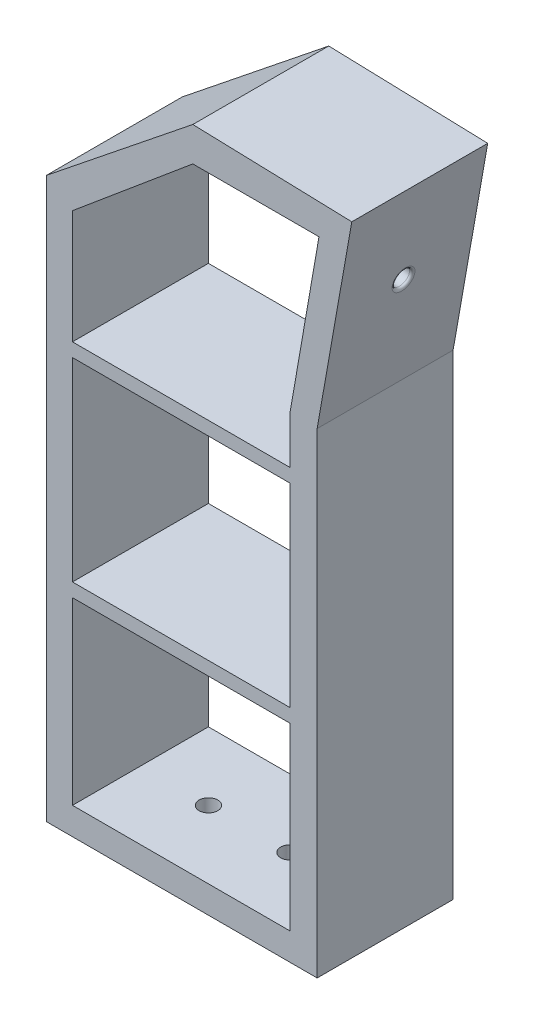
SolidWorks part; units mm, degrees
ref_plane "Front Plane" through (0, 0, 0) normal (0, 0, 1) x (1, 0, 0)
ref_plane "Top Plane" through (0, 0, 0) normal (0, 1, 0) x (1, 0, 0)
ref_plane "Right Plane" through (0, 0, 0) normal (1, 0, 0) x (0, 0, -1)
sketch "Sketch2" plane through (0, 0, 0) normal (0, 0, 1) x (1, 0, 0)
  line L8 (-40.5065, 0) -> (59.131, 0)
  line L10 (59.131, 232.5877) -> (59.801, 236.4462)
  line L12 (59.131, 0) -> (59.131, 175)
  line L14 (59.131, 175) -> (59.131, 265.8716) construction
  line L16 (-40.869, 107.9897) -> (-30.869, 107.9897) construction
  line L17 (65.5005, 211.1233) -> (55.5005, 211.1233) construction
  line L18 (59.131, 87.5) -> (49.131, 87.5) construction
  line L19 (0, 0) -> (0, 10) construction
  line L20 (0, 10) -> (49.131, 10)
  line L21 (49.131, 10) -> (49.131, 87.5)
  line L22 (49.131, 87.5) -> (49.131, 175)
  line L23 (-40.5065, 205.8291) -> (-40.5065, 0)
  line L28 (-30.869, 107.9897) -> (-30.869, 10)
  line L29 (-30.869, 10) -> (0, 10)
  line L30 (59.131, 175) -> (71.87, 247.2467)
  line L32 (-30.869, 107.9897) -> (-30.869, 199.4173)
  line L34 (59.131, 232.5877) -> (49.131, 175)
  line L35 (59.131, 232.5877) -> (68.9791, 230.8512) construction
  line L36 (71.87, 247.2467) -> (13.3973, 249.0046)
  line L37 (13.3973, 249.0046) -> (-40.5065, 205.8291)
  line L38 (42.6337, 248.1256) -> (42.6337, 236.4462) construction
  line L39 (-30.869, 199.4173) -> (6.2516, 230.4687)
  line L40 (59.801, 236.4462) -> (42.6337, 236.4462)
  line L41 (42.6337, 236.4462) -> (13.3973, 236.4462)
  line L44 (13.3973, 249.0046) -> (13.3973, 239.0046) construction
  line L46 (0, 238.2737) -> (6.2516, 230.4687) construction
  line L47 (6.2516, 230.4687) -> (13.3973, 236.4462)
  point P1 (9.131, 107.9897)
  dimension "D1" = 10
  dimension "D2" = 9.131
  dimension "D3" = 49.131
  dimension "D4" = 59.131
  dimension "D5" = 71.87
  dimension "D6" = 30.869
  dimension "D7" = 40.5065
  dimension "D8" = 175
extrude "Boss-Extrude1" add sketch "Sketch2" along normal blind 50
sketch "Sketch10" plane through (0, 10, 0) normal (0, 1, 0) x (1, 0, 0)
  line L0 (49.131, -25) -> (24.131, -25) construction
  line L1 (-30.869, -50) -> (-30.869, 0) construction
  line L3 (-30.869, -25) -> (-5.8513, -25) construction
  line L4 (49.131, -50) -> (49.131, 0) construction
  circle A0 centre (-5.8513, -25) radius 3.425
  circle A1 centre (24.131, -25) radius 3.425
  dimension "D1" = 6.85
  dimension "D2" = 6.85
  dimension "D3" = 25.0177
  dimension "D4" = 55
extrude "Cut-Extrude5" cut sketch "Sketch10" against normal blind 10
sketch "Sketch11" plane through (0, 0, 50) normal (0, 0, 1) x (1, 0, 0)
  line L1 (-30.869, 157.6357) -> (49.131, 157.6357)
  line L2 (49.131, 10) -> (49.131, 175) construction
  line L6 (-30.869, 10) -> (-30.869, 81.1513) construction
  line L7 (-30.869, 81.1513) -> (-30.869, 157.6357) construction
  line L8 (-30.869, 199.4173) -> (-30.869, 10) construction
  line L9 (49.131, 157.6357) -> (49.131, 152.6357)
  line L10 (49.131, 152.6357) -> (-30.869, 152.6357)
  line L11 (-30.869, 152.6357) -> (-30.869, 157.6357)
  line L12 (-30.869, 81.1513) -> (49.131, 81.1513)
  line L13 (49.131, 81.1513) -> (49.131, 76.1513)
  line L14 (49.131, 76.1513) -> (-30.869, 76.1513)
  line L15 (-30.869, 76.1513) -> (-30.869, 81.1513)
  line L17 (-40.5065, 0) -> (59.131, 0) construction
  dimension "D1" = 5
  dimension "D2" = 5
  dimension "D3" = 76.1513
  dimension "D4" = 152.6357
extrude "Boss-Extrude3" add sketch "Sketch11" against normal blind 50
sketch "Sketch14" plane through (27.4212, -4.8351, 0) normal (0.9848, -0.1736, 0) x (0, 0, -1)
  line L0 (-25, 182.6093) -> (-25, 221.6093) construction
  line L1 (-50, 182.6093) -> (0, 182.6093) construction
  circle A0 centre (-25, 221.6093) radius 3.15
  dimension "D1" = 6.3
extrude "Cut-Extrude6" cut sketch "Sketch14" against normal blind 10
fillet "Fillet1" radius 1 1 edges at (66.4502, 216.5096, 25)
